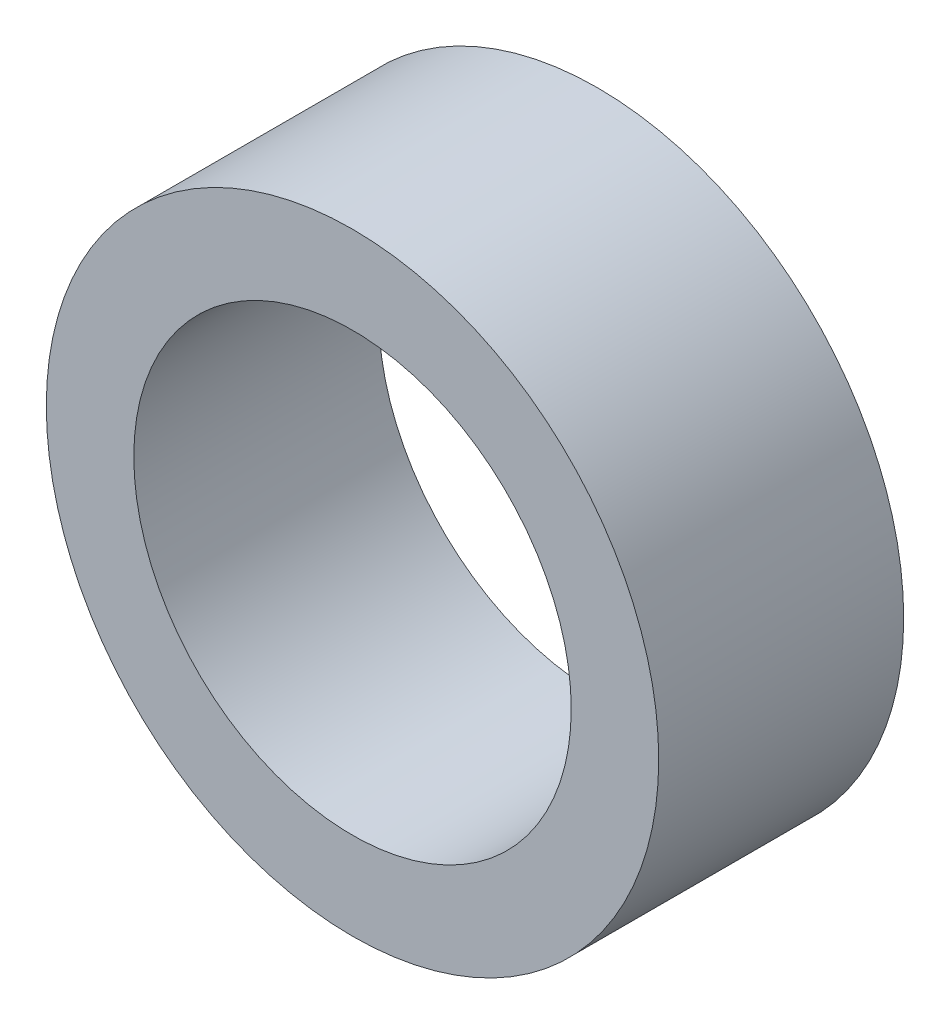
SolidWorks part; units mm, degrees
ref_plane "前视基准面" through (0, 0, 0) normal (0, 0, 1) x (1, 0, 0)
ref_plane "上视基准面" through (0, 0, 0) normal (0, 1, 0) x (1, 0, 0)
ref_plane "右视基准面" through (0, 0, 0) normal (1, 0, 0) x (0, 0, -1)
sketch "草图1" plane through (0, 0, 0) normal (0, 0, 1) x (1, 0, 0)
  circle A0 centre (0, 0) radius 3.5
  circle A1 centre (0, 0) radius 2.5
  dimension "D1" = 7
  dimension "D2" = 5
extrude "凸台-拉伸1" add sketch "草图1" along normal blind 2.8
